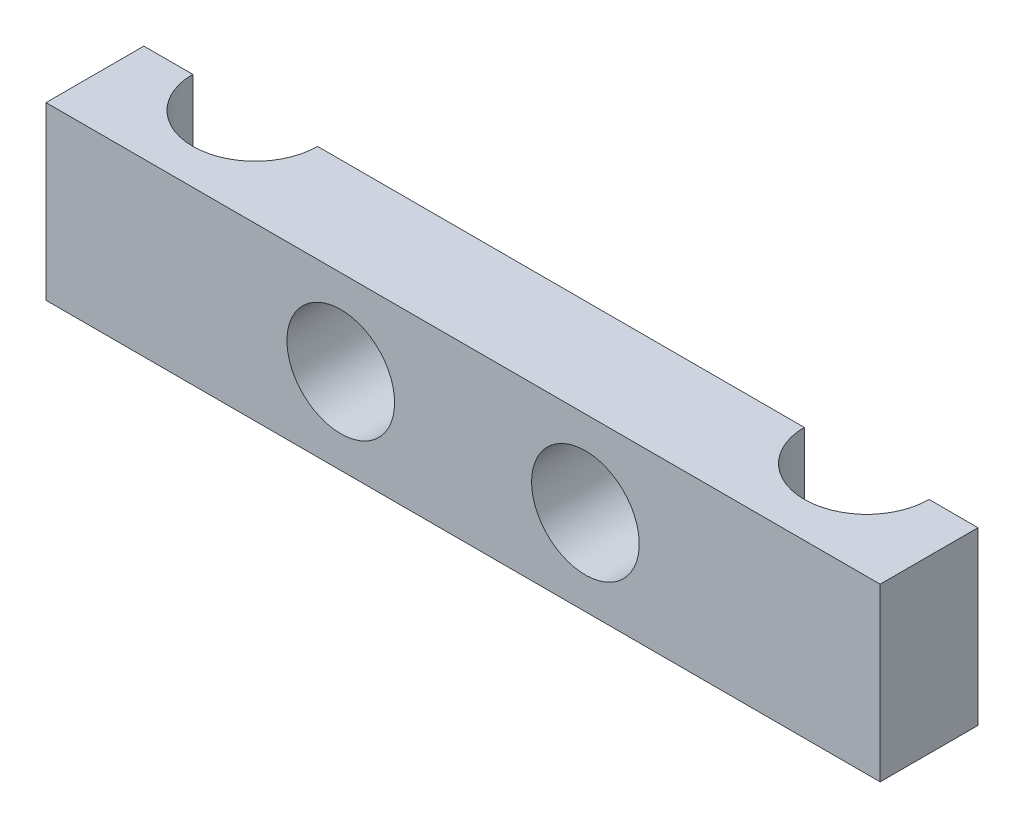
SolidWorks part; units mm, degrees
ref_plane "Front Plane" through (0, 0, 0) normal (0, 0, 1) x (1, 0, 0)
ref_plane "Top Plane" through (0, 0, 0) normal (0, 1, 0) x (1, 0, 0)
ref_plane "Right Plane" through (0, 0, 0) normal (1, 0, 0) x (0, 0, -1)
sketch "Sketch1" plane through (0, 0, 0) normal (0, 1, 0) x (1, 0, 0)
  line L0 (0, 0) -> (-17.05, 0)
  line L1 (-17.05, 0) -> (-17.05, 4)
  line L2 (-17.05, 4) -> (-15.05, 4)
  line L3 (0, 0) -> (0, 4)
  line L4 (0, 4) -> (-9.95, 4)
  arc A0 (-15.05, 4) -> (-9.95, 4) centre (-12.5, 4) ccw
  dimension "D1" = 2.55
  dimension "D2" = 12.5
  dimension "D3" = 2
  dimension "D4" = 4
extrude "Boss-Extrude1" add sketch "Sketch1" along normal blind 7
sketch "Sketch2" plane through (0, 0, 0) normal (0, 0, 1) x (1, 0, 0)
  line L0 (0, 7) -> (0, 0) construction
  circle A0 centre (-5, 3.5) radius 2.2
  point P6 (0, 3.5)
  dimension "D1" = 4.4
  dimension "D2" = 5
extrude "Cut-Extrude1" cut sketch "Sketch2" against normal up to surface (4 mm away) up to face at (-4.975, 3.5, -4)
mirror "Mirror1" about plane through (0, 0, 0) normal (1, 0, 0) of bodies 102
